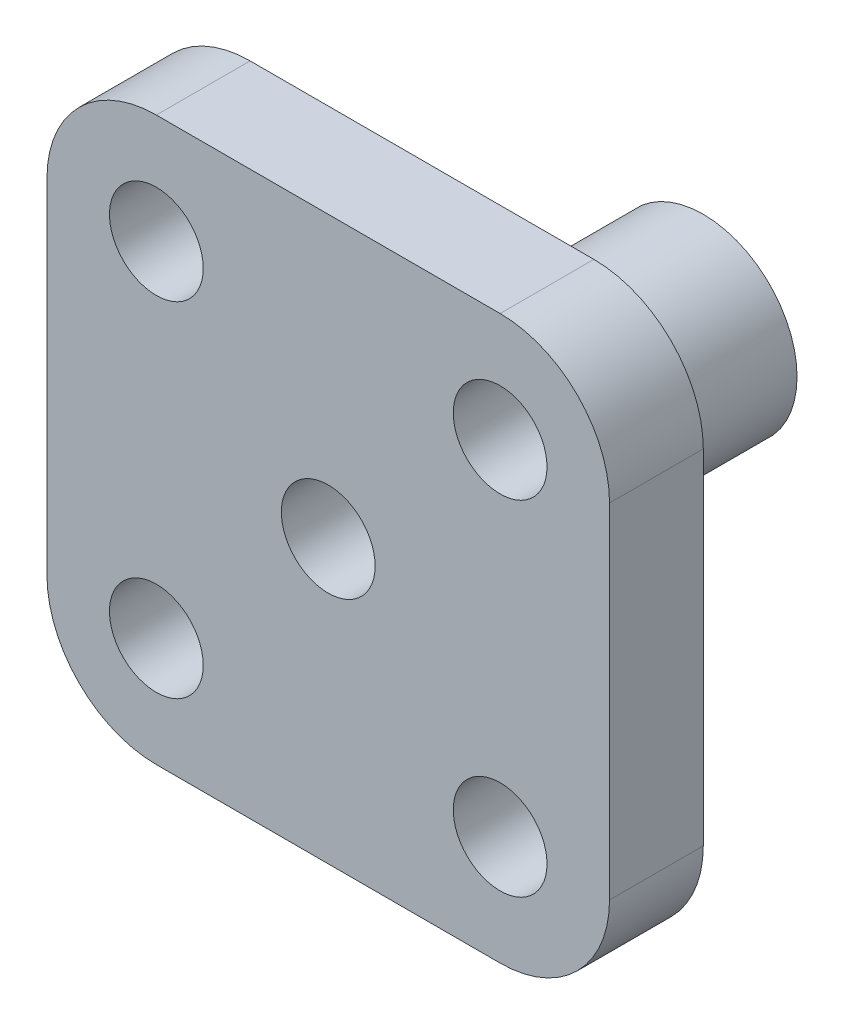
SolidWorks part; units mm, degrees
ref_plane "Front" through (0, 0, 0) normal (0, 0, 1) x (1, 0, 0)
ref_plane "Top" through (0, 0, 0) normal (0, 1, 0) x (1, 0, 0)
ref_plane "Right" through (0, 0, 0) normal (1, 0, 0) x (0, 0, -1)
sketch "Sketch1" plane through (0, 0, 0) normal (0, 1, 0) x (1, 0, 0)
  line L0 (0, 2.8839) -> (0, -1.9864) construction
  line L1 (0, 2.25) -> (0.75, 2.25)
  line L2 (0.75, 2.25) -> (0.75, 0)
  line L3 (0.75, 0) -> (0, 0)
  line L4 (0, 2.25) -> (0, 0)
  point P5 (0.75, 1.5299)
  point P8 (0, 2.8839)
  dimension "D1" = 0.75
  dimension "D2" = 2.25
revolve "Revolve1" add sketch "Sketch1" angle 360 about L0
sketch "Sketch2" plane through (0, 0, 0) normal (0, 0, 1) x (1, 0, 0)
  line L1 (2.25, -2.25) -> (-2.25, -2.25)
  line L2 (2.25, -2.25) -> (2.25, 2.25)
  line L3 (2.25, 2.25) -> (-2.25, 2.25)
  line L4 (-2.25, -2.25) -> (-2.25, 2.25)
  line L5 (2.25, -2.25) -> (-2.25, 2.25) construction
  line L6 (2.25, 2.25) -> (-2.25, -2.25) construction
  point P0 (0, 0)
  dimension "D1" = 4.5
  dimension "D2" = 4.5
extrude "Boss-Extrude1" add sketch "Sketch2" along normal blind 0.75
fillet "Fillet2" radius 0.875 4 edges at (2.25, -2.25, 0.375) (-2.25, -2.25, 0.375) (-2.25, 2.25, 0.375) (2.25, 2.25, 0.375)
sketch "Sketch6" plane through (0, 0, 0.75) normal (0, 0, 1) x (1, 0, 0)
  circle A0 centre (-1.375, 1.375) radius 0.375
  circle A1 centre (1.375, 1.375) radius 0.375
  circle A2 centre (0, 0) radius 0.375
  circle A3 centre (-1.375, -1.375) radius 0.375
  circle A4 centre (1.375, -1.375) radius 0.375
  dimension "D1" = 0.75
extrude "Cut-Extrude1" cut sketch "Sketch6" against normal blind 0.75 contours A0 | A1 | A2 | A3 | A4
sketch "Sketch9" plane through (0, 0, -2.25) normal (0, 0, -1) x (-1, 0, 0)
  circle A0 centre (0, 0) radius 0.6562
  dimension "D1" = 1.3125
extrude "Cut-Extrude2" cut sketch "Sketch9" against normal blind 2.25
